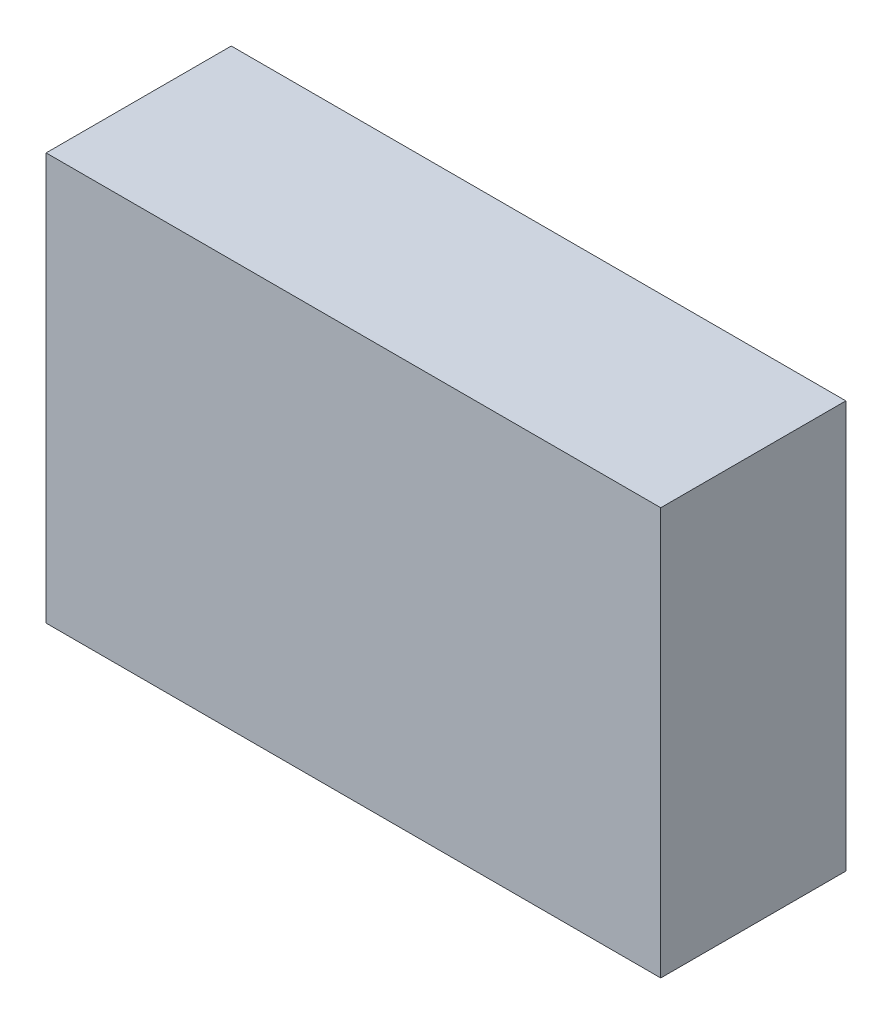
SolidWorks part; units mm, degrees
ref_plane "Přední rovina" through (0, 0, 0) normal (0, 0, 1) x (1, 0, 0)
ref_plane "Horní rovina" through (0, 0, 0) normal (0, 1, 0) x (1, 0, 0)
ref_plane "Pravá rovina" through (0, 0, 0) normal (1, 0, 0) x (0, 0, -1)
sketch "Skica1" plane through (0, 0, 0) normal (0, 0, 1) x (1, 0, 0)
  line L1 (0, 0) -> (166, 0)
  line L2 (0, 0) -> (0, 110)
  line L3 (0, 110) -> (166, 110)
  line L4 (166, 0) -> (166, 110)
  dimension "D1" = 110
  dimension "D2" = 166
extrude "Přidat vysunutím1" add sketch "Skica1" along normal blind 50
